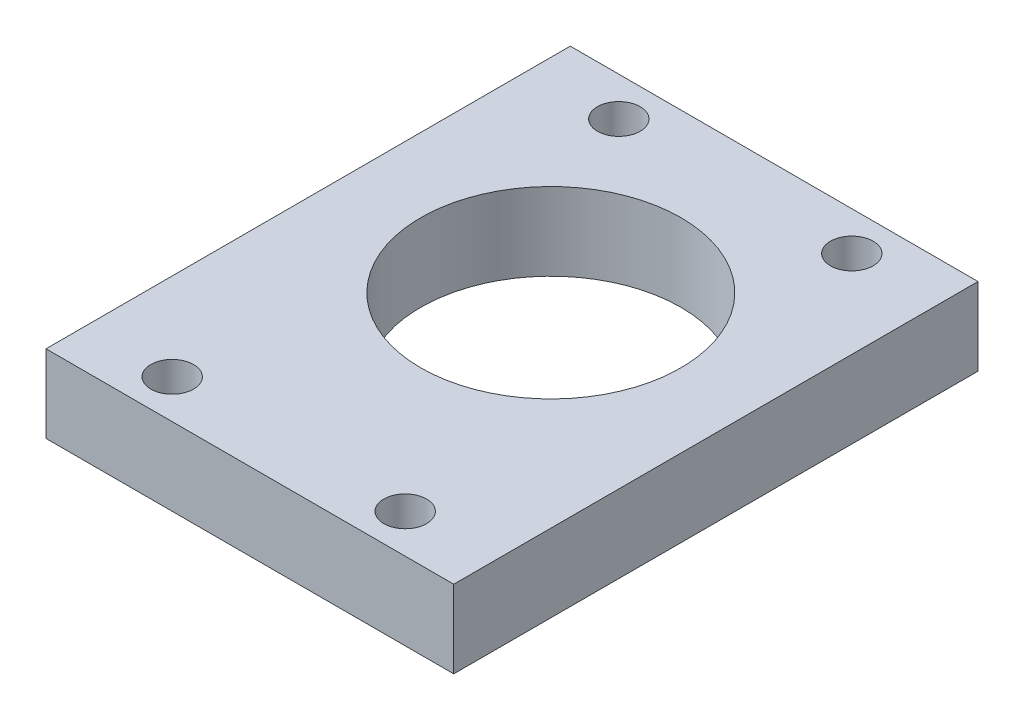
SolidWorks part; units mm, degrees
material "Alliage 1060"
ref_plane "Plan de face" through (0, 0, 0) normal (0, 0, 1) x (1, 0, 0)
ref_plane "Plan de dessus" through (0, 0, 0) normal (0, 1, 0) x (1, 0, 0)
ref_plane "Plan de droite" through (0, 0, 0) normal (1, 0, 0) x (0, 0, -1)
sketch "Esquisse1" plane through (0, 0, 0) normal (0, 1, 0) x (1, 0, 0)
  line L0 (0, 31) -> (42, 31) construction
  line L1 (0, 0) -> (42, 0)
  line L2 (0, 0) -> (0, 62)
  line L3 (0, 62) -> (42, 62)
  line L4 (42, 0) -> (42, 62)
  circle A0 centre (21, 31) radius 13.4
  point P10 (21, 31)
  dimension "D1" = 26.8
  dimension "D4" = 42
  dimension "D5" = 62
extrude "Boss.-Extru.1" add sketch "Esquisse1" along normal blind 8
sketch "Esquisse3" plane through (0, 8, 0) normal (0, 1, 0) x (1, 0, 0)
  line L0 (42, 0) -> (42, 62) construction
  line L1 (0, 62) -> (42, 62)
  line L2 (0, 62) -> (0, 54)
  line L3 (0, 54) -> (42, 54)
  line L4 (42, 62) -> (42, 54)
  dimension "D1" = 8
extrude "Enlèv. mat.-Extru.2" cut sketch "Esquisse3" against normal up to next
sketch "Esquisse2" plane through (0, 8, 0) normal (0, 1, 0) x (1, 0, 0)
  line L0 (9, 50) -> (33, 50) construction
  line L2 (0, 54) -> (0, 0) construction
  line L3 (0, 54) -> (42, 54) construction
  line L4 (21, 54) -> (21, 50) construction
  line L5 (0, 27) -> (42, 27) construction
  line L6 (42, 0) -> (42, 54) construction
  circle A0 centre (9, 50) radius 2.2
  circle A1 centre (33, 50) radius 2.2
  circle A2 centre (33, 4) radius 2.2
  circle A3 centre (9, 4) radius 2.2
  point P21 (21, 54)
  dimension "D1" = 4.4
  dimension "D2" = 4
  dimension "D3" = 9
extrude "Enlèv. mat.-Extru.1" cut sketch "Esquisse2" against normal through all
